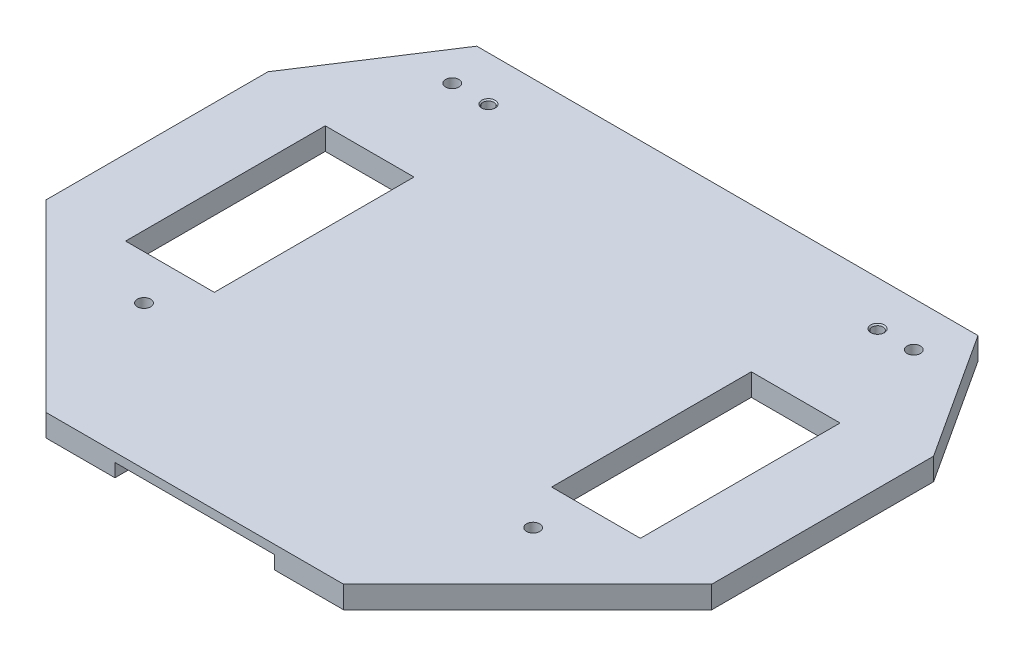
SolidWorks part; units mm, degrees
material "PMMA"
ref_plane "Front Plane" through (0, 0, 0) normal (0, 0, 1) x (1, 0, 0)
ref_plane "Top Plane" through (0, 0, 0) normal (0, 1, 0) x (1, 0, 0)
ref_plane "Right Plane" through (0, 0, 0) normal (1, 0, 0) x (0, 0, -1)
sketch "Sketch3" plane through (0, -40, 0) normal (0, -1, 0) x (-1, 0, 0)
  line L1 (18.4686, -110) -> (85.5327, -110)
  line L2 (-23, -68.5314) -> (-23, -18.5314)
  line L3 (-4.4715, 10) -> (108.4727, 10)
  line L4 (127, -68.5327) -> (127, -18.5295)
  line L5 (108.4727, 10) -> (127, -18.5295)
  line L6 (108.1379, 10.5156) -> (115.3271, -0.5548) construction
  line L7 (-4.4715, 10) -> (-23, -18.5314)
  line L8 (-17.9432, -10.7447) -> (2.4807, 20.7055) construction
  line L9 (127, -68.5327) -> (85.5327, -110)
  line L10 (52.0006, 10) -> (52.0006, -110) construction
  line L11 (18.4686, -110) -> (-23, -68.5314)
  dimension "D1" = 150
  dimension "D2" = 10
  dimension "D3" = 23
  dimension "D4" = 120
  dimension "D5" = 135
  dimension "D6" = 135
  dimension "D7" = 33
  dimension "D8" = 33
  dimension "D9" = 50
extrude "Boss-Extrude1" add sketch "Sketch3" along normal blind 5
hole_wizard "Ø3.0 (3) Diameter Hole1" positions "Sketch5" profile "Sketch4" hole size "Ø3.0" standard "ANSI Metric"
sketch "Sketch5" plane through (0, -45, 0) normal (0, -1, 0) x (-1, 0, 0)
  circle A0 centre (8.157, -77.6082) radius 1.5 construction
  circle A1 centre (95.8382, -77.6082) radius 1.5 construction
  circle A2 centre (103.9952, 0) radius 1.5 construction
  circle A3 centre (0, 0) radius 1.5 construction
  point P0 (8.157, -77.6082)
  point P3 (95.8382, -77.6082)
  point P6 (103.9952, 0)
  point P9 (0, 0)
sketch "Sketch4" plane through (-8.157, -45, 77.6082) normal (1, 0, 0) x (0, 0, -1)
  line L0 (0, 0) -> (0, 6.9013)
  line L1 (0, 6.9013) -> (1.5, 6)
  line L2 (1.5, 6) -> (1.5, 0)
  line L5 (1.5, 0) -> (0, 0)
  line L10 (0, 6.9013) -> (-1.5, 6) construction
  line L11 (0, -6.35) -> (0, 107.95) construction
  dimension "Hole Dia." = 3
  dimension "Hole Depth" = 6
  dimension "Drill Angle" = 118
sketch "Sketch6" plane through (0, -45, 0) normal (0, -1, 0) x (-1, 0, 0)
  line L0 (-23, -18.5314) -> (-23, -68.5314) construction
  line L1 (34, 7) -> (70, 7)
  line L2 (34, 7) -> (34, -117)
  line L3 (34, -117) -> (70, -117)
  line L4 (70, 7) -> (70, -117)
  line L6 (108.4727, 10) -> (-4.4715, 10) construction
  dimension "D1" = 124
  dimension "D2" = 36
  dimension "D3" = 57
  dimension "D4" = 3
extrude "Cut-Extrude1" cut sketch "Sketch6" against normal blind 3
sketch "Sketch9" plane through (0, -45, 0) normal (0, -1, 0) x (-1, 0, 0)
  line L1 (-6, -22.6082) -> (14, -22.6082)
  line L2 (-6, -22.6082) -> (-6, -67.6082)
  line L3 (-6, -67.6082) -> (14, -67.6082)
  line L4 (14, -22.6082) -> (14, -67.6082)
  line L5 (34, 7) -> (34, -110) construction
  dimension "D1" = 45
  dimension "D2" = 10
  dimension "D3" = 20
  dimension "D4" = 20
extrude "Cut-Extrude3" cut sketch "Sketch9" against normal through all
ref_plane "Plane2" through (-52, 0, 0) normal (-1, 0, 0) x (0, 0, 1)
mirror "Mirror1" about plane through (-52, 0, 0) normal (-1, 0, 0) of "Cut-Extrude3"
sketch "Sketch10" plane through (0, -40, 0) normal (0, 1, 0) x (1, 0, 0)
  line L1 (-8.157, -77.6082) -> (-95.8382, -77.6082) construction
  line L2 (-8.157, -77.6082) -> (-8.157, 0) construction
  line L3 (-8.157, 0) -> (-95.8382, 0) construction
  line L4 (-95.8382, -77.6082) -> (-95.8382, 0) construction
hole_wizard "M3x0.5 Tapped Hole1" positions "Sketch12" profile "Sketch11" tap size "M3x0.5" standard "ANSI Metric" end condition up to next
sketch "Sketch12" plane through (0, -40, 0) normal (0, 1, 0) x (1, 0, 0)
  point P0 (-8.157, 0)
  point P3 (-95.8382, 0)
sketch "Sketch11" plane through (-8.157, -40, 0) normal (1, 0, 0) x (0, 0, 1)
  line L0 (0, 0) -> (0, 5)
  line L1 (0, 5) -> (1.25, 5)
  line L2 (1.25, 5) -> (1.25, 0.275)
  line L3 (1.25, 0.275) -> (1.525, 0)
  line L5 (1.525, 0) -> (0, 0)
  line L6 (-1.25, 0.275) -> (-1.525, 0) construction
  line L11 (0, -6.35) -> (0, 107.95) construction
  dimension "Thru Tap Drill Dia." = 2.5
  dimension "Thru Tap Drill Depth" = 5
  dimension "Near C'Sink Dia." = 3.05
  dimension "Near C'Sink Angle" = 90
cosmetic thread "Hole Thread1" parameters "D2"=3
cosmetic thread "Hole Thread2" parameters "D2"=3
